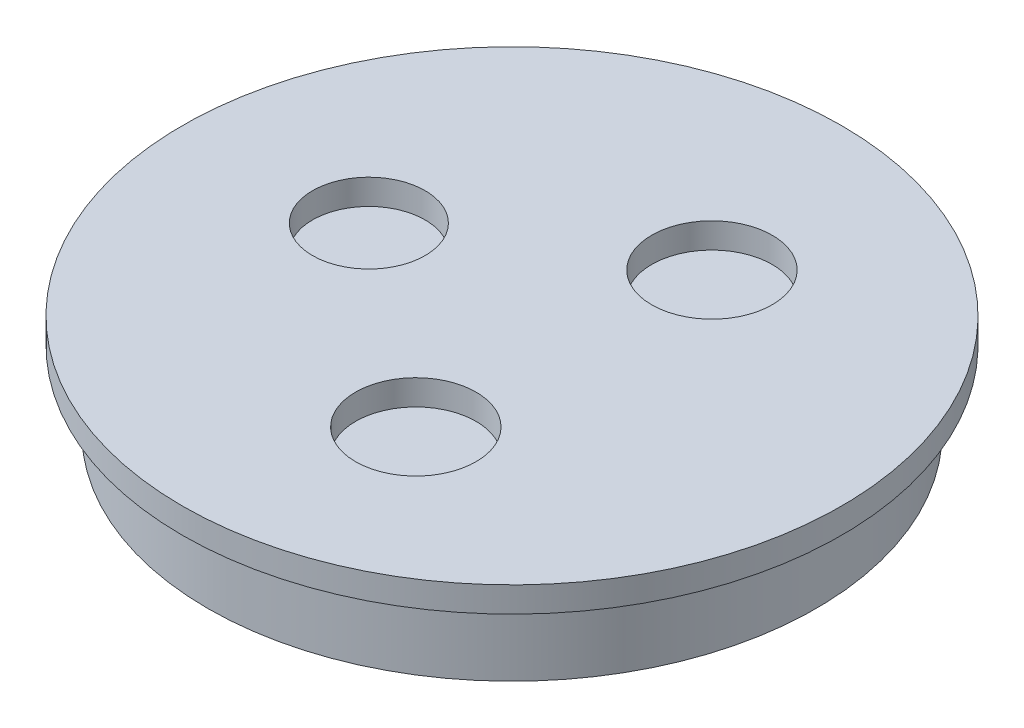
SolidWorks part; units mm, degrees
material "Acrylic (Medium-high impact)"
ref_plane "Front Plane" through (0, 0, 0) normal (0, 0, 1) x (1, 0, 0)
ref_plane "Top Plane" through (0, 0, 0) normal (0, 1, 0) x (1, 0, 0)
ref_plane "Right Plane" through (0, 0, 0) normal (1, 0, 0) x (0, 0, -1)
sketch "Sketch1" plane through (0, 0, 0) normal (0, 1, 0) x (1, 0, 0)
  circle A0 centre (0, 0) radius 38.1 construction
  circle A1 centre (0, 0) radius 41.275
  circle A2 centre (0, 0) radius 19.05 construction
  circle A3 centre (-19.0188, 1.089) radius 7.05
  circle A4 centre (6.0257, -18.0719) radius 7.55
  circle A5 centre (7.5508, 17.4896) radius 7.55
  dimension "D1" = 76.2
  dimension "D2" = 82.55
  dimension "D3" = 14.1
  dimension "D4" = 15.1
  dimension "D5" = 15.1
  dimension "D6" = 38.1
extrude "Boss-Extrude1" add sketch "Sketch1" along normal blind 3.175
sketch "Sketch2" plane through (0, 0, 0) normal (0, -1, 0) x (1, 0, 0)
  circle A0 centre (0, 0) radius 38.1
  dimension "D1" = 76.2
extrude "Boss-Extrude2" add sketch "Sketch2" along normal blind 9.525
